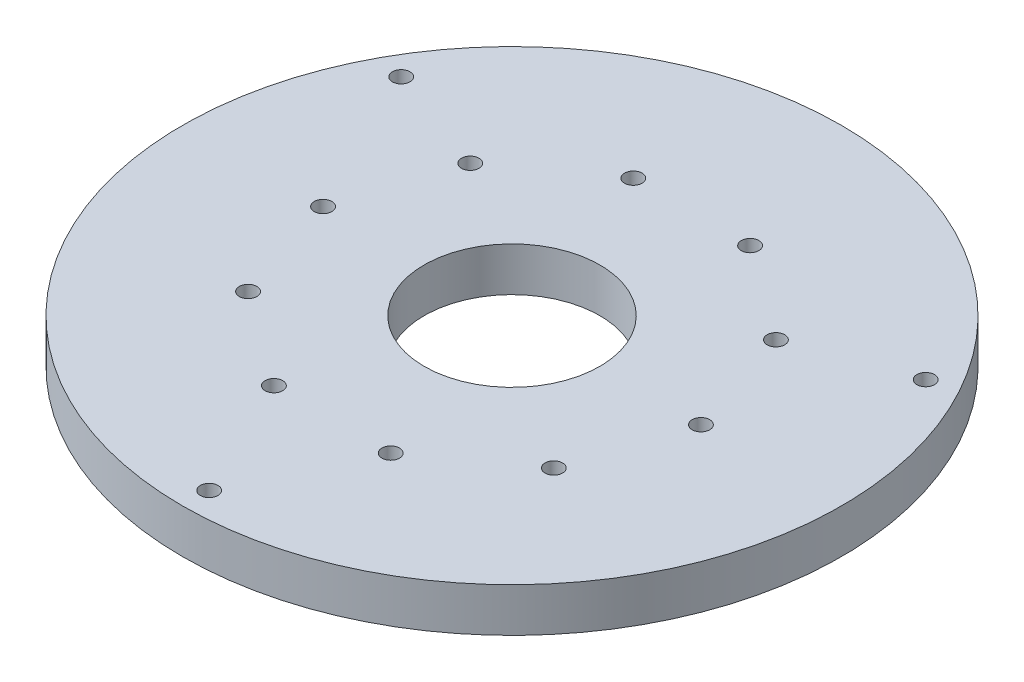
SolidWorks part; units mm, degrees
ref_plane "Front Plane" through (0, 0, 0) normal (0, 0, 1) x (1, 0, 0)
ref_plane "Top Plane" through (0, 0, 0) normal (0, 1, 0) x (1, 0, 0)
ref_plane "Right Plane" through (0, 0, 0) normal (1, 0, 0) x (0, 0, -1)
sketch "Sketch1" plane through (0, 0, 0) normal (0, 1, 0) x (1, 0, 0)
  circle A0 centre (0, 0) radius 37.5
  dimension "D1" = 75
extrude "Boss-Extrude1" add sketch "Sketch1" against normal blind 5
sketch "Sketch2" plane through (0, 0, 0) normal (0, 1, 0) x (1, 0, 0)
  line L0 (-2.75, 0) -> (2.75, 0) construction
  line L1 (0, 39.8902) -> (0, -39.5701) construction
  line L2 (0, -2.75) -> (0, 2.75) construction
  line L4 (-39.7283, 0) -> (39.0263, 0) construction
  circle A0 centre (-21.5, 0) radius 1
  circle A1 centre (-17.3939, 12.6374) radius 1
  circle A2 centre (-6.6439, 20.4477) radius 1
  circle A3 centre (6.6439, 20.4477) radius 1
  circle A4 centre (17.3939, 12.6374) radius 1
  circle A5 centre (21.5, 0) radius 1
  circle A6 centre (17.3939, -12.6374) radius 1
  circle A7 centre (6.6439, -20.4477) radius 1
  circle A8 centre (-6.6439, -20.4477) radius 1
  circle A9 centre (-17.3939, -12.6374) radius 1
  dimension "D1" = 10
  dimension "D2" = 43
extrude "Cut-Extrude1" cut sketch "Sketch2" against normal up to next
sketch "Sketch4" plane through (0, -5, 0) normal (0, -1, 0) x (1, 0, 0)
  line L0 (-15.5255, 11.28) -> (-15.2841, 13.5767)
  line L1 (-19.1906, 0) -> (-20.3453, 2)
  line L2 (-20.3453, 2) -> (-22.6547, 2)
  line L3 (-22.6547, 2) -> (-23.8094, 0)
  line L4 (-23.8094, 0) -> (-22.6547, -2)
  line L5 (-22.6547, -2) -> (-20.3453, -2)
  line L6 (-20.3453, -2) -> (-19.1906, 0)
  line L7 (-15.2841, 13.5767) -> (-17.1525, 14.9341)
  line L8 (-17.1525, 14.9341) -> (-19.2622, 13.9948)
  line L9 (-19.2622, 13.9948) -> (-19.5036, 11.6981)
  line L10 (-19.5036, 11.6981) -> (-17.6353, 10.3406)
  line L11 (-17.6353, 10.3406) -> (-15.5255, 11.28)
  line L12 (-5.9302, 18.2513) -> (-4.3849, 19.9676)
  line L13 (-4.3849, 19.9676) -> (-5.0986, 22.1639)
  line L14 (-5.0986, 22.1639) -> (-7.3575, 22.6441)
  line L15 (-7.3575, 22.6441) -> (-8.9028, 20.9279)
  line L16 (-8.9028, 20.9279) -> (-8.1892, 18.7315)
  line L17 (-8.1892, 18.7315) -> (-5.9302, 18.2513)
  line L18 (5.9302, 18.2513) -> (8.1892, 18.7315)
  line L19 (8.1892, 18.7315) -> (8.9028, 20.9279)
  line L20 (8.9028, 20.9279) -> (7.3575, 22.6441)
  line L21 (7.3575, 22.6441) -> (5.0986, 22.1639)
  line L22 (5.0986, 22.1639) -> (4.3849, 19.9676)
  line L23 (4.3849, 19.9676) -> (5.9302, 18.2513)
  line L24 (15.5255, 11.28) -> (17.6353, 10.3406)
  line L25 (17.6353, 10.3406) -> (19.5036, 11.6981)
  line L26 (19.5036, 11.6981) -> (19.2622, 13.9948)
  line L27 (19.2622, 13.9948) -> (17.1525, 14.9341)
  line L28 (17.1525, 14.9341) -> (15.2841, 13.5767)
  line L29 (15.2841, 13.5767) -> (15.5255, 11.28)
  line L30 (19.1906, 0) -> (20.3453, -2)
  line L31 (20.3453, -2) -> (22.6547, -2)
  line L32 (22.6547, -2) -> (23.8094, 0)
  line L33 (23.8094, 0) -> (22.6547, 2)
  line L34 (22.6547, 2) -> (20.3453, 2)
  line L35 (20.3453, 2) -> (19.1906, 0)
  line L36 (15.5255, -11.28) -> (15.2841, -13.5767)
  line L37 (15.2841, -13.5767) -> (17.1525, -14.9341)
  line L38 (17.1525, -14.9341) -> (19.2622, -13.9948)
  line L39 (19.2622, -13.9948) -> (19.5036, -11.6981)
  line L40 (19.5036, -11.6981) -> (17.6353, -10.3406)
  line L41 (17.6353, -10.3406) -> (15.5255, -11.28)
  line L42 (5.9302, -18.2513) -> (4.3849, -19.9676)
  line L43 (4.3849, -19.9676) -> (5.0986, -22.1639)
  line L44 (5.0986, -22.1639) -> (7.3575, -22.6441)
  line L45 (7.3575, -22.6441) -> (8.9028, -20.9279)
  line L46 (8.9028, -20.9279) -> (8.1892, -18.7315)
  line L47 (8.1892, -18.7315) -> (5.9302, -18.2513)
  line L48 (-5.9302, -18.2513) -> (-8.1892, -18.7315)
  line L49 (-8.1892, -18.7315) -> (-8.9028, -20.9279)
  line L50 (-8.9028, -20.9279) -> (-7.3575, -22.6441)
  line L51 (-7.3575, -22.6441) -> (-5.0986, -22.1639)
  line L52 (-5.0986, -22.1639) -> (-4.3849, -19.9676)
  line L53 (-4.3849, -19.9676) -> (-5.9302, -18.2513)
  line L54 (-15.5255, -11.28) -> (-17.6353, -10.3406)
  line L55 (-17.6353, -10.3406) -> (-19.5036, -11.6981)
  line L56 (-19.5036, -11.6981) -> (-19.2622, -13.9948)
  line L57 (-19.2622, -13.9948) -> (-17.1525, -14.9341)
  line L58 (-17.1525, -14.9341) -> (-15.2841, -13.5767)
  line L59 (-15.2841, -13.5767) -> (-15.5255, -11.28)
  circle A0 centre (-21.5, 0) radius 2 construction
  dimension "D1" = 10
extrude "Cut-Extrude2" cut sketch "Sketch4" against normal blind 1.6
sketch "Sketch6" plane through (0, 0, 0) normal (0, 1, 0) x (1, 0, 0)
  circle A0 centre (0, 0) radius 10
extrude "Cut-Extrude3" cut sketch "Sketch6" against normal up to next
sketch "Sketch7" plane through (0, 0, 0) normal (0, 1, 0) x (1, 0, 0)
  line L0 (0, -32.4389) -> (0, -37.9681) construction
  line L1 (-3, -37.3798) -> (3, -37.3798) construction
  line L2 (-3, -37.3798) -> (-3, -31.5382) construction
  line L3 (-3, -31.5382) -> (3, -31.5382) construction
  line L4 (3, -37.3798) -> (3, -31.5382) construction
  line L5 (0, -2.75) -> (0, 2.75) construction
  line L6 (-3.8774, -34.459) -> (4.357, -34.459) construction
  circle A0 centre (0, 0) radius 37.5 construction
  circle A1 centre (0, -34.459) radius 1
  circle A2 centre (-29.8424, 17.2295) radius 1
  circle A3 centre (29.8424, 17.2295) radius 1
  dimension "D1" = 3
extrude "Cut-Extrude4" cut sketch "Sketch7" against normal up to surface (5 mm away) up to face at (0, -5, 10)
